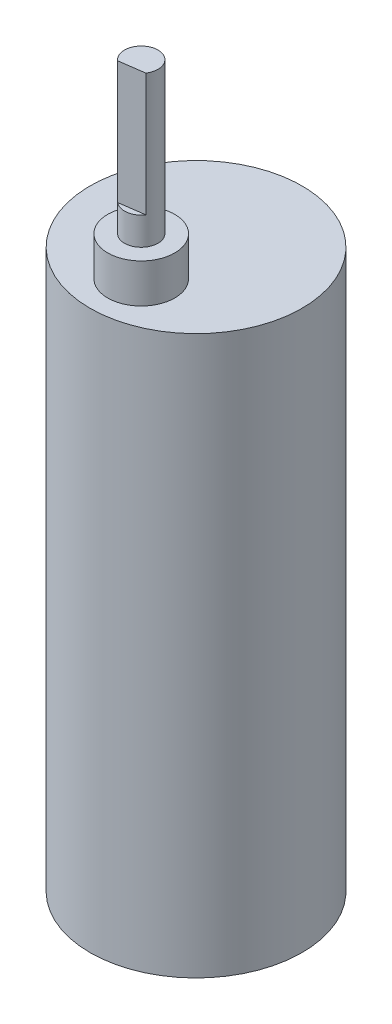
SolidWorks part; units mm, degrees
ref_plane "Front Plane" through (0, 0, 0) normal (0, 0, 1) x (1, 0, 0)
ref_plane "Top Plane" through (0, 0, 0) normal (0, 1, 0) x (1, 0, 0)
ref_plane "Right Plane" through (0, 0, 0) normal (1, 0, 0) x (0, 0, -1)
sketch "Sketch1" plane through (0, 0, 0) normal (0, 1, 0) x (1, 0, 0)
  circle A0 centre (0, 0) radius 19
  point P2 (0, 0)
  dimension "D1" = 38
extrude "Boss-Extrude1" add sketch "Sketch1" along normal blind 100
sketch "Sketch2" plane through (0, 100, 0) normal (0, 1, 0) x (1, 0, 0)
  line L0 (0, -19) -> (0, -15.825)
  line L1 (0, -15.825) -> (0, -9.825) construction
  circle A1 centre (0, 0) radius 19 construction
  circle A2 centre (0, -9.825) radius 6
  dimension "D1" = 3.175
  dimension "D2" = 6
extrude "Boss-Extrude2" add sketch "Sketch2" along normal blind 7 contours A2
sketch "Sketch3" plane through (0, 107, 0) normal (0, 1, 0) x (1, 0, 0)
  circle A0 centre (0, -9.825) radius 3
  circle A1 centre (0, -9.825) radius 6 construction
  dimension "D1" = 6
extrude "Boss-Extrude3" add sketch "Sketch3" along normal blind 27
sketch "Sketch4" plane through (0, 134, 0) normal (0, 1, 0) x (1, 0, 0)
  line L0 (-9.1506, -13.1351) -> (10.8494, -10.315)
  line L1 (-9.011, -14.1253) -> (10.989, -11.3052)
  line L2 (10.8494, -10.315) -> (10.989, -11.3052)
  line L3 (-9.1506, -13.1351) -> (-9.011, -14.1253)
  circle A0 centre (0, -9.825) radius 3 construction
  dimension "D1" = 1
  dimension "D2" = 20
extrude "Cut-Extrude1" cut sketch "Sketch4" against normal blind 22
